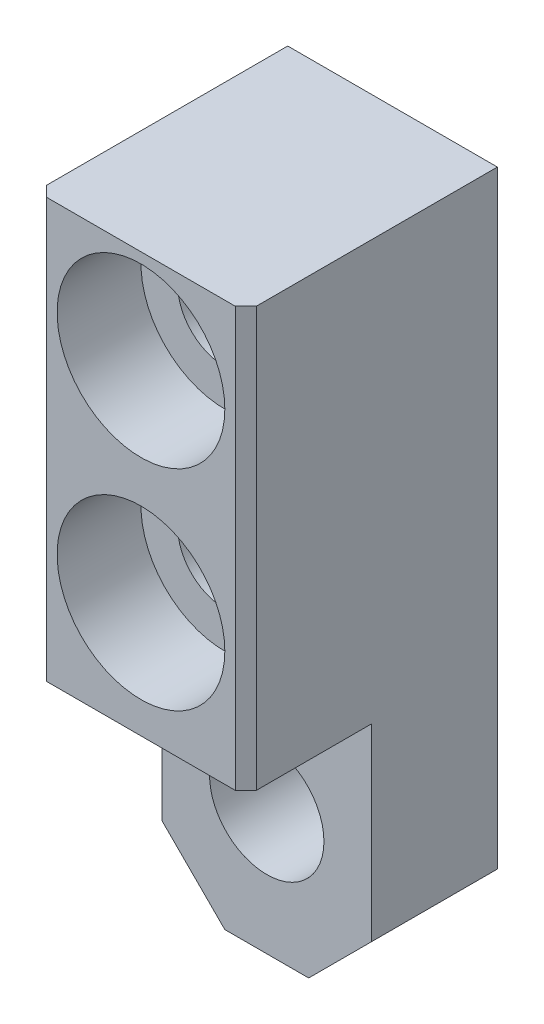
SolidWorks part; units mm, degrees
ref_plane "Front Plane" through (0, 0, 0) normal (0, 0, 1) x (1, 0, 0)
ref_plane "Top Plane" through (0, 0, 0) normal (0, 1, 0) x (1, 0, 0)
ref_plane "Right Plane" through (0, 0, 0) normal (1, 0, 0) x (0, 0, -1)
sketch "Sketch1" plane through (0, 0, 0) normal (0, 0, 1) x (1, 0, 0)
  line L1 (0, 0) -> (10, 0)
  line L2 (0, 0) -> (0, -32)
  line L3 (0, -32) -> (10, -32)
  line L4 (10, 0) -> (10, -32)
  dimension "D1" = 10
  dimension "D2" = 32
extrude "Boss-Extrude1" add sketch "Sketch1" along normal blind 6
sketch "Sketch2" plane through (0, 0, 6) normal (0, 0, 1) x (1, 0, 0)
  line L0 (10, -32) -> (10, 0) construction
  line L1 (0, 0) -> (10, 0)
  line L2 (0, 0) -> (0, -20)
  line L3 (0, -20) -> (10, -20)
  line L4 (10, 0) -> (10, -20)
  dimension "D1" = 20
extrude "Boss-Extrude2" add sketch "Sketch2" along normal blind 6
sketch "Sketch3" plane through (0, 0, 12) normal (0, 0, 1) x (1, 0, 0)
  line L0 (10, 0) -> (0, 0) construction
  circle A0 centre (5, -4.5) radius 2.25
  circle A1 centre (5, -14.5) radius 2.25
  point P4 (0, 0)
  point P7 (5, 0)
  dimension "D3" = 4.5
  dimension "D1" = 4.5
  dimension "D2" = 14.5
extrude "Cut-Extrude1" cut sketch "Sketch3" against normal through all
sketch "Sketch4" plane through (0, 0, 12) normal (0, 0, 1) x (1, 0, 0)
  circle A0 centre (5, -4.5) radius 4
  circle A1 centre (5, -14.5) radius 4
  dimension "D1" = 8
  dimension "D2" = 8
extrude "Cut-Extrude2" cut sketch "Sketch4" against normal blind 4
chamfer "Chamfer1" distance 3 angle 45 2 edges at (10, -32, 3) (0, -32, 3)
chamfer "Chamfer2" distance 0.5 angle 45 2 edges at (10, -10, 12) (0, -10, 12)
sketch "Sketch5" plane through (0, 0, 6) normal (0, 0, 1) x (1, 0, 0)
  line L0 (9.5, 0) -> (0.5, 0) construction
  circle A0 centre (5, -26) radius 2.7272
  dimension "D1" = 26
extrude "Cut-Extrude3" cut sketch "Sketch5" against normal through all
